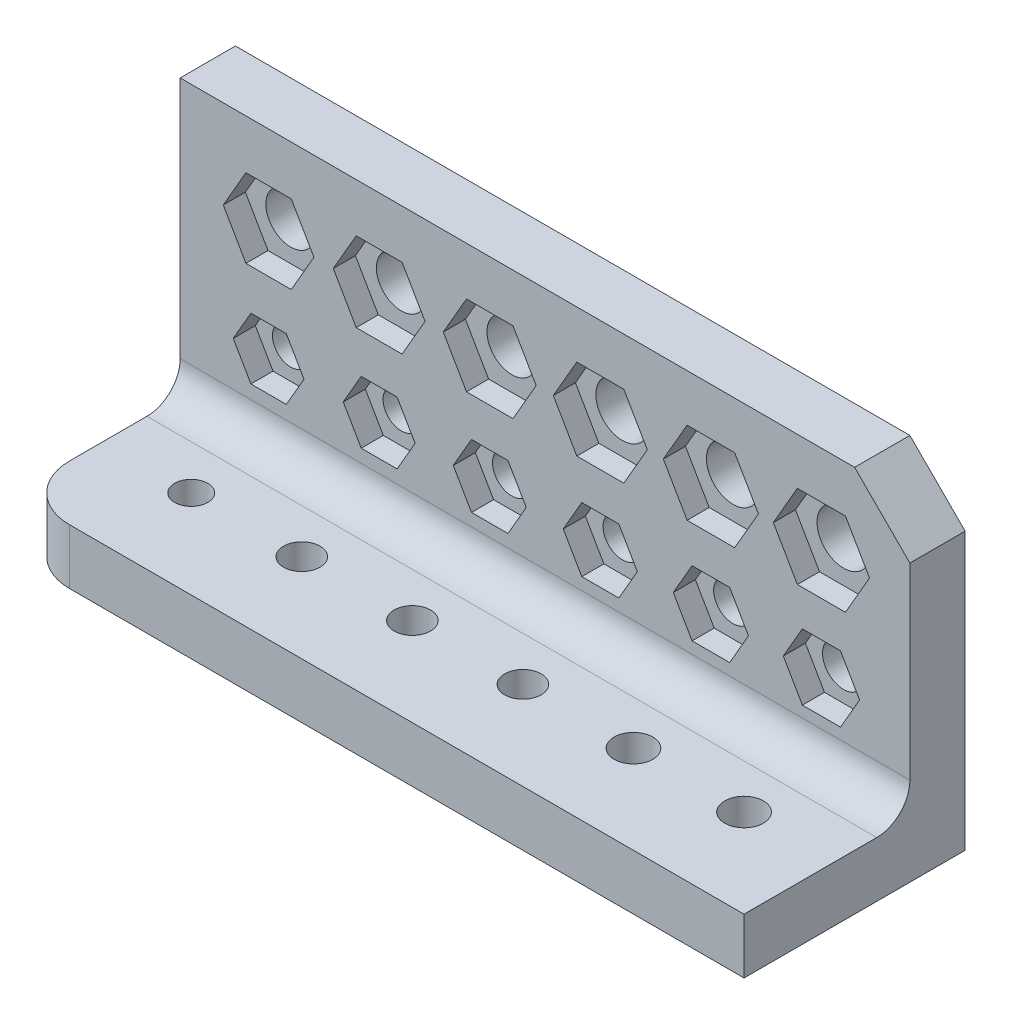
SolidWorks part; units mm, degrees
ref_plane "前视基准面" through (0, 0, 0) normal (0, 0, 1) x (1, 0, 0)
ref_plane "上视基准面" through (0, 0, 0) normal (0, 1, 0) x (1, 0, 0)
ref_plane "右视基准面" through (0, 0, 0) normal (1, 0, 0) x (0, 0, -1)
ref_plane "基准面4" through (0, 0, 0) normal (0, 0, -1) x (-1, 0, 0)
sketch "草图1" plane through (0, 0, 0) normal (0, 0, -1) x (-1, 0, 0)
  line L0 (0, 30) -> (-66, 30)
  line L1 (-66, 30) -> (-66, 0)
  line L2 (-66, 0) -> (0, 0)
  line L3 (0, 0) -> (0, 30)
extrude "凸台-拉伸1" add sketch "草图1" against normal blind 20
sketch "草图2" plane through (0, 0, 0) normal (-1, 0, 0) x (0, 0, 1)
  line L0 (20, 30) -> (5, 30)
  line L1 (5, 30) -> (5, 5)
  line L2 (5, 5) -> (20, 5)
  line L3 (20, 5) -> (20, 30)
extrude "切除-拉伸1" cut sketch "草图2" against normal through all
sketch "草图3" plane through (0, 0, 0) normal (0, -1, 0) x (1, 0, 0)
  line L0 (58.1427, 8.5029) -> (61.0999, 10.375)
  line L1 (61.0999, 10.375) -> (60.9572, 13.8721)
  line L2 (60.9572, 13.8721) -> (57.8573, 15.4971)
  line L3 (57.8573, 15.4971) -> (54.9001, 13.625)
  line L4 (54.9001, 13.625) -> (55.0428, 10.1279)
  line L5 (55.0428, 10.1279) -> (58.1427, 8.5029)
extrude "切除-拉伸2" cut sketch "草图3" against normal blind 2
sketch "草图4" plane through (0, 0, 0) normal (0, -1, 0) x (1, 0, 0)
  line L0 (48.1144, 8.5519) -> (51.0433, 10.375)
  line L1 (51.0433, 10.375) -> (50.929, 13.8231)
  line L2 (50.929, 13.8231) -> (47.8856, 15.4481)
  line L3 (47.8856, 15.4481) -> (44.9567, 13.625)
  line L4 (44.9567, 13.625) -> (45.071, 10.1769)
  line L5 (45.071, 10.1769) -> (48.1144, 8.5519)
extrude "切除-拉伸3" cut sketch "草图4" against normal blind 2
sketch "草图5" plane through (0, 0, 0) normal (0, -1, 0) x (1, 0, 0)
  line L0 (38.086, 8.6011) -> (40.9865, 10.375)
  line L1 (40.9865, 10.375) -> (40.9006, 13.7739)
  line L2 (40.9006, 13.7739) -> (37.914, 15.3989)
  line L3 (37.914, 15.3989) -> (35.0135, 13.625)
  line L4 (35.0135, 13.625) -> (35.0994, 10.2261)
  line L5 (35.0994, 10.2261) -> (38.086, 8.6011)
extrude "切除-拉伸4" cut sketch "草图5" against normal blind 2
sketch "草图6" plane through (0, 0, 0) normal (0, -1, 0) x (1, 0, 0)
  line L0 (28.0575, 8.6505) -> (30.9295, 10.375)
  line L1 (30.9295, 10.375) -> (30.872, 13.7245)
  line L2 (30.872, 13.7245) -> (27.9425, 15.3495)
  line L3 (27.9425, 15.3495) -> (25.0705, 13.625)
  line L4 (25.0705, 13.625) -> (25.128, 10.2755)
  line L5 (25.128, 10.2755) -> (28.0575, 8.6505)
extrude "切除-拉伸5" cut sketch "草图6" against normal blind 2
sketch "草图7" plane through (0, 0, 0) normal (0, -1, 0) x (1, 0, 0)
  line L0 (18.0288, 8.7001) -> (20.8722, 10.375)
  line L1 (20.8722, 10.375) -> (20.8434, 13.6749)
  line L2 (20.8434, 13.6749) -> (17.9712, 15.2999)
  line L3 (17.9712, 15.2999) -> (15.1278, 13.625)
  line L4 (15.1278, 13.625) -> (15.1566, 10.3251)
  line L5 (15.1566, 10.3251) -> (18.0288, 8.7001)
extrude "切除-拉伸6" cut sketch "草图7" against normal blind 2
sketch "草图8" plane through (0, 0, 0) normal (0, -1, 0) x (1, 0, 0)
  line L0 (8, 8.75) -> (10.8146, 10.375)
  line L1 (10.8146, 10.375) -> (10.8146, 13.625)
  line L2 (10.8146, 13.625) -> (8, 15.25)
  line L3 (8, 15.25) -> (5.1854, 13.625)
  line L4 (5.1854, 13.625) -> (5.1854, 10.375)
  line L5 (5.1854, 10.375) -> (8, 8.75)
extrude "切除-拉伸7" cut sketch "草图8" against normal blind 2
sketch "草图9" plane through (0, 0, 5) normal (0, 0, 1) x (1, 0, 0)
  line L0 (10.05, 18.4493) -> (12.1, 22)
  line L1 (12.1, 22) -> (10.05, 25.5507)
  line L2 (10.05, 25.5507) -> (5.95, 25.5507)
  line L3 (5.95, 25.5507) -> (3.9, 22)
  line L4 (3.9, 22) -> (5.95, 18.4493)
  line L5 (5.95, 18.4493) -> (10.05, 18.4493)
extrude "切除-拉伸8" cut sketch "草图9" against normal blind 2
sketch "草图10" plane through (0, 0, 5) normal (0, 0, 1) x (1, 0, 0)
  line L0 (9.6, 9.2287) -> (11.2, 12)
  line L1 (11.2, 12) -> (9.6, 14.7713)
  line L2 (9.6, 14.7713) -> (6.4, 14.7713)
  line L3 (6.4, 14.7713) -> (4.8, 12)
  line L4 (4.8, 12) -> (6.4, 9.2287)
  line L5 (6.4, 9.2287) -> (9.6, 9.2287)
extrude "切除-拉伸9" cut sketch "草图10" against normal blind 2
sketch "草图11" plane through (0, 0, 5) normal (0, 0, 1) x (1, 0, 0)
  line L0 (19.625, 9.1854) -> (21.25, 12)
  line L1 (21.25, 12) -> (19.625, 14.8146)
  line L2 (19.625, 14.8146) -> (16.375, 14.8146)
  line L3 (16.375, 14.8146) -> (14.75, 12)
  line L4 (14.75, 12) -> (16.375, 9.1854)
  line L5 (16.375, 9.1854) -> (19.625, 9.1854)
extrude "切除-拉伸10" cut sketch "草图11" against normal blind 2
sketch "草图12" plane through (0, 0, 5) normal (0, 0, 1) x (1, 0, 0)
  line L0 (29.65, 9.1421) -> (31.3, 12)
  line L1 (31.3, 12) -> (29.65, 14.8579)
  line L2 (29.65, 14.8579) -> (26.35, 14.8579)
  line L3 (26.35, 14.8579) -> (24.7, 12)
  line L4 (24.7, 12) -> (26.35, 9.1421)
  line L5 (26.35, 9.1421) -> (29.65, 9.1421)
extrude "切除-拉伸11" cut sketch "草图12" against normal blind 2
sketch "草图13" plane through (0, 0, 5) normal (0, 0, 1) x (1, 0, 0)
  line L0 (20.075, 18.406) -> (22.15, 22)
  line L1 (22.15, 22) -> (20.075, 25.594)
  line L2 (20.075, 25.594) -> (15.925, 25.594)
  line L3 (15.925, 25.594) -> (13.85, 22)
  line L4 (13.85, 22) -> (15.925, 18.406)
  line L5 (15.925, 18.406) -> (20.075, 18.406)
extrude "切除-拉伸12" cut sketch "草图13" against normal blind 2
sketch "草图14" plane through (0, 0, 5) normal (0, 0, 1) x (1, 0, 0)
  line L0 (30.1, 18.3627) -> (32.2, 22)
  line L1 (32.2, 22) -> (30.1, 25.6373)
  line L2 (30.1, 25.6373) -> (25.9, 25.6373)
  line L3 (25.9, 25.6373) -> (23.8, 22)
  line L4 (23.8, 22) -> (25.9, 18.3627)
  line L5 (25.9, 18.3627) -> (30.1, 18.3627)
extrude "切除-拉伸13" cut sketch "草图14" against normal blind 2
sketch "草图15" plane through (0, 0, 5) normal (0, 0, 1) x (1, 0, 0)
  line L0 (40.125, 18.3194) -> (42.25, 22)
  line L1 (42.25, 22) -> (40.125, 25.6806)
  line L2 (40.125, 25.6806) -> (35.875, 25.6806)
  line L3 (35.875, 25.6806) -> (33.75, 22)
  line L4 (33.75, 22) -> (35.875, 18.3194)
  line L5 (35.875, 18.3194) -> (40.125, 18.3194)
extrude "切除-拉伸14" cut sketch "草图15" against normal blind 2
sketch "草图16" plane through (0, 0, 5) normal (0, 0, 1) x (1, 0, 0)
  line L0 (50.15, 18.2761) -> (52.3, 22)
  line L1 (52.3, 22) -> (50.15, 25.7239)
  line L2 (50.15, 25.7239) -> (45.85, 25.7239)
  line L3 (45.85, 25.7239) -> (43.7, 22)
  line L4 (43.7, 22) -> (45.85, 18.2761)
  line L5 (45.85, 18.2761) -> (50.15, 18.2761)
extrude "切除-拉伸15" cut sketch "草图16" against normal blind 2
sketch "草图17" plane through (0, 0, 5) normal (0, 0, 1) x (1, 0, 0)
  line L0 (60.175, 18.2328) -> (62.35, 22)
  line L1 (62.35, 22) -> (60.175, 25.7672)
  line L2 (60.175, 25.7672) -> (55.825, 25.7672)
  line L3 (55.825, 25.7672) -> (53.65, 22)
  line L4 (53.65, 22) -> (55.825, 18.2328)
  line L5 (55.825, 18.2328) -> (60.175, 18.2328)
extrude "切除-拉伸16" cut sketch "草图17" against normal blind 2
sketch "草图18" plane through (0, 0, 5) normal (0, 0, 1) x (1, 0, 0)
  line L0 (59.725, 9.0122) -> (61.45, 12)
  line L1 (61.45, 12) -> (59.725, 14.9878)
  line L2 (59.725, 14.9878) -> (56.275, 14.9878)
  line L3 (56.275, 14.9878) -> (54.55, 12)
  line L4 (54.55, 12) -> (56.275, 9.0122)
  line L5 (56.275, 9.0122) -> (59.725, 9.0122)
extrude "切除-拉伸17" cut sketch "草图18" against normal blind 2
sketch "草图19" plane through (0, 0, 5) normal (0, 0, 1) x (1, 0, 0)
  line L0 (49.7, 9.0555) -> (51.4, 12)
  line L1 (51.4, 12) -> (49.7, 14.9445)
  line L2 (49.7, 14.9445) -> (46.3, 14.9445)
  line L3 (46.3, 14.9445) -> (44.6, 12)
  line L4 (44.6, 12) -> (46.3, 9.0555)
  line L5 (46.3, 9.0555) -> (49.7, 9.0555)
extrude "切除-拉伸18" cut sketch "草图19" against normal blind 2
sketch "草图20" plane through (0, 0, 5) normal (0, 0, 1) x (1, 0, 0)
  line L0 (39.675, 9.0988) -> (41.35, 12)
  line L1 (41.35, 12) -> (39.675, 14.9012)
  line L2 (39.675, 14.9012) -> (36.325, 14.9012)
  line L3 (36.325, 14.9012) -> (34.65, 12)
  line L4 (34.65, 12) -> (36.325, 9.0988)
  line L5 (36.325, 9.0988) -> (39.675, 9.0988)
extrude "切除-拉伸19" cut sketch "草图20" against normal blind 2
hole_wizard "Ø3.0 (3) 直径孔1" positions "草图22" profile "草图21" hole size "Ø3.0" standard "ANSI Metric"
sketch "草图22" plane through (0, 5, 0) normal (0, 1, 0) x (1, 0, 0)
  point P0 (8, -12)
sketch "草图21" plane through (8, 5, 12) normal (1, 0, 0) x (0, 0, 1)
  line L0 (0, 0) -> (0, 5)
  line L1 (0, 5) -> (1.5, 5)
  line L2 (1.5, 5) -> (1.5, 0)
  line L5 (1.5, 0) -> (0, 0)
  line L11 (0, -6.35) -> (0, 107.95) construction
  dimension "通孔孔直径" = 3
  dimension "通孔孔深度" = 5
hole_wizard "Ø3.3 (3.3) 直径孔1" positions "草图24" profile "草图23" hole size "Ø3.3" standard "ANSI Metric"
sketch "草图24" plane through (0, 5, 0) normal (0, 1, 0) x (1, 0, 0)
  point P0 (38, -12)
  point P1 (28, -12)
  point P2 (18, -12)
sketch "草图23" plane through (38, 5, 12) normal (1, 0, 0) x (0, 0, 1)
  line L0 (0, 0) -> (0, 5)
  line L1 (0, 5) -> (1.65, 5)
  line L2 (1.65, 5) -> (1.65, 0)
  line L5 (1.65, 0) -> (0, 0)
  line L11 (0, -6.35) -> (0, 107.95) construction
  dimension "通孔孔直径" = 3.3
  dimension "通孔孔深度" = 5
hole_wizard "Ø3.5 (3.5) 直径孔1" positions "草图26" profile "草图25" hole size "Ø3.5" standard "ANSI Metric"
sketch "草图26" plane through (0, 5, 0) normal (0, 1, 0) x (1, 0, 0)
  point P0 (58, -12)
  point P1 (48, -12)
sketch "草图25" plane through (58, 5, 12) normal (1, 0, 0) x (0, 0, 1)
  line L0 (0, 0) -> (0, 5)
  line L1 (0, 5) -> (1.75, 5)
  line L2 (1.75, 5) -> (1.75, 0)
  line L5 (1.75, 0) -> (0, 0)
  line L11 (0, -6.35) -> (0, 107.95) construction
  dimension "通孔孔直径" = 3.5
  dimension "通孔孔深度" = 5
hole_wizard "Ø3.8 (3.8) 直径孔1" positions "草图28" profile "草图27" hole size "Ø3.8" standard "ANSI Metric"
sketch "草图28" plane through (0, 0, 0) normal (0, 0, -1) x (-1, 0, 0)
  point P0 (-58, 12)
sketch "草图27" plane through (58, 12, 0) normal (1, 0, 0) x (0, 1, 0)
  line L0 (0, 0) -> (0, 20)
  line L1 (0, 20) -> (1.9, 20)
  line L2 (1.9, 20) -> (1.9, 0)
  line L5 (1.9, 0) -> (0, 0)
  line L11 (0, -6.35) -> (0, 107.95) construction
  dimension "通孔孔直径" = 3.8
  dimension "通孔孔深度" = 20
hole_wizard "Ø4.5 (4.5) 直径孔1" positions "草图30" profile "草图29" hole size "Ø4.5" standard "ANSI Metric"
sketch "草图30" plane through (0, 0, 0) normal (0, 0, -1) x (-1, 0, 0)
  point P0 (-28, 22)
  point P1 (-18, 22)
  point P2 (-8, 22)
sketch "草图29" plane through (28, 22, 0) normal (1, 0, 0) x (0, 1, 0)
  line L0 (0, 0) -> (0, 20)
  line L1 (0, 20) -> (2.25, 20)
  line L2 (2.25, 20) -> (2.25, 0)
  line L5 (2.25, 0) -> (0, 0)
  line L11 (0, -6.35) -> (0, 107.95) construction
  dimension "通孔孔直径" = 4.5
  dimension "通孔孔深度" = 20
hole_wizard "Ø3.5 (3.5) 直径孔2" positions "草图32" profile "草图31" hole size "Ø3.5" standard "ANSI Metric"
sketch "草图32" plane through (0, 0, 0) normal (0, 0, -1) x (-1, 0, 0)
  point P0 (-28, 12)
  point P1 (-38, 12)
  point P2 (-48, 12)
sketch "草图31" plane through (28, 12, 0) normal (1, 0, 0) x (0, 1, 0)
  line L0 (0, 0) -> (0, 20)
  line L1 (0, 20) -> (1.75, 20)
  line L2 (1.75, 20) -> (1.75, 0)
  line L5 (1.75, 0) -> (0, 0)
  line L11 (0, -6.35) -> (0, 107.95) construction
  dimension "通孔孔直径" = 3.5
  dimension "通孔孔深度" = 20
hole_wizard "Ø4.8 (4.8) 直径孔1" positions "草图34" profile "草图33" hole size "Ø4.8" standard "ANSI Metric"
sketch "草图34" plane through (0, 0, 0) normal (0, 0, -1) x (-1, 0, 0)
  point P0 (-58, 22)
  point P1 (-48, 22)
  point P2 (-38, 22)
sketch "草图33" plane through (58, 22, 0) normal (1, 0, 0) x (0, 1, 0)
  line L0 (0, 0) -> (0, 20)
  line L1 (0, 20) -> (2.4, 20)
  line L2 (2.4, 20) -> (2.4, 0)
  line L5 (2.4, 0) -> (0, 0)
  line L11 (0, -6.35) -> (0, 107.95) construction
  dimension "通孔孔直径" = 4.8
  dimension "通孔孔深度" = 20
hole_wizard "Ø3.3 (3.3) 直径孔2" positions "草图36" profile "草图35" hole size "Ø3.3" standard "ANSI Metric"
sketch "草图36" plane through (0, 0, 0) normal (0, 0, -1) x (-1, 0, 0)
  point P0 (-8, 12)
  point P1 (-18, 12)
sketch "草图35" plane through (8, 12, 0) normal (1, 0, 0) x (0, 1, 0)
  line L0 (0, 0) -> (0, 20)
  line L1 (0, 20) -> (1.65, 20)
  line L2 (1.65, 20) -> (1.65, 0)
  line L5 (1.65, 0) -> (0, 0)
  line L11 (0, -6.35) -> (0, 107.95) construction
  dimension "通孔孔直径" = 3.3
  dimension "通孔孔深度" = 20
chamfer "倒角1" distance 5 angle 45 1 edges at (66, 30, 2.5)
fillet "圆角1" radius 3 1 edges at (33, 5, 5)
fillet "圆角2" radius 5 1 edges at (0, 2.5, 20)
